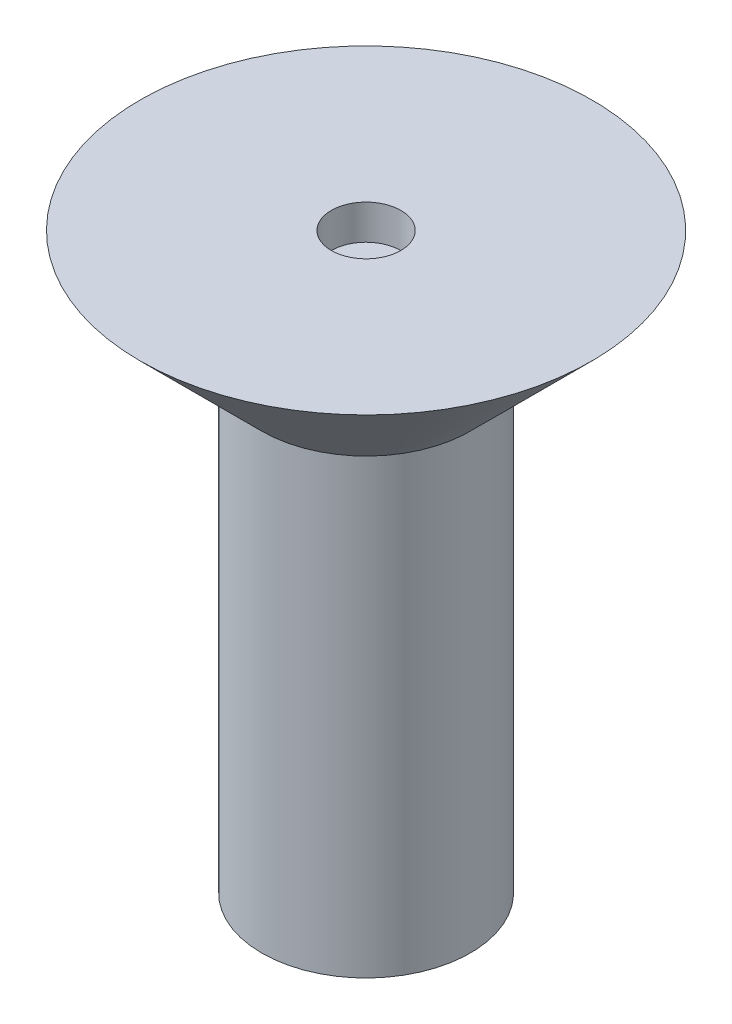
SolidWorks part; units mm, degrees
ref_plane "Front Plane" through (0, 0, 0) normal (0, 0, 1) x (1, 0, 0)
ref_plane "Top Plane" through (0, 0, 0) normal (0, 1, 0) x (1, 0, 0)
ref_plane "Right Plane" through (0, 0, 0) normal (1, 0, 0) x (0, 0, -1)
sketch "Sketch1" plane through (0, 0, 0) normal (0, 0, 1) x (1, 0, 0)
  line L0 (0, 81.8643) -> (0, -64.5662) construction
  line L1 (0, 0) -> (-3, 0)
  line L2 (-3, 0) -> (0, -1.7321)
  line L3 (-3, 0) -> (-3, 13)
  line L4 (-3, 13) -> (-6.5, 16.5)
  line L5 (-6.5, 16.5) -> (0, 16.5)
  line L6 (-1, 16.5) -> (-1, 15.5)
  line L7 (-1, 15.5) -> (0, 15.5)
  dimension "D1" = 13
  dimension "D2" = 60
  dimension "D3" = 3
  dimension "D4" = 45
  dimension "D5" = 6.5
  dimension "D6" = 1
  dimension "D7" = 1
revolve "Revolve1" add sketch "Sketch1" angle 360 about L0
